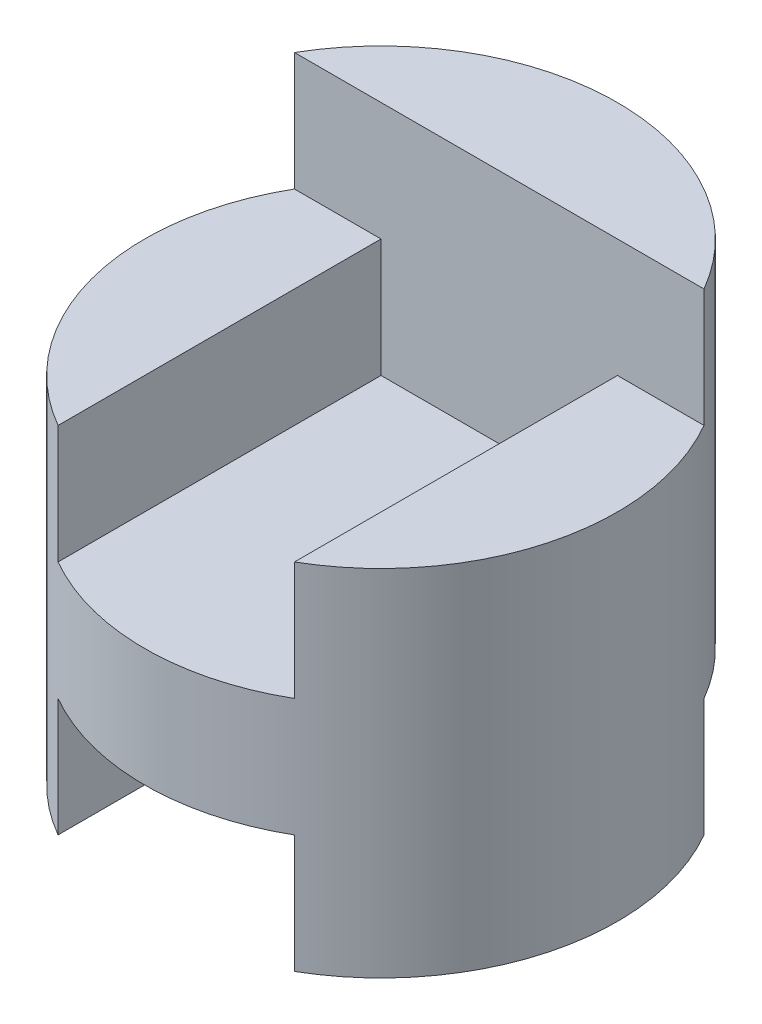
SolidWorks part; units mm, degrees
ref_plane "Front" through (0, 0, 0) normal (0, 0, 1) x (1, 0, 0)
ref_plane "Top" through (0, 0, 0) normal (0, 1, 0) x (1, 0, 0)
ref_plane "Right" through (0, 0, 0) normal (1, 0, 0) x (0, 0, -1)
sketch "Sketch1" plane through (0, 0, 0) normal (0, 1, 0) x (1, 0, 0)
  circle A0 centre (0, 0) radius 2
  dimension "D1" = 4
extrude "Boss-Extrude1" add sketch "Sketch1" along normal blind 4
sketch "Sketch2" plane through (0, 0, 0) normal (0, 0, 1) x (1, 0, 0)
  line L0 (-1, 1) -> (1, 1)
  line L4 (-1, 0) -> (-1, 1)
  line L16 (1, 0) -> (1, 1)
  line L17 (1, 0) -> (-1, 0)
  dimension "D4" = 1
extrude "Cut-Extrude1" cut sketch "Sketch2" against normal mid plane 4
sketch "Sketch3" plane through (0, 0, 0) normal (0, 0, 1) x (1, 0, 0)
  line L0 (-2, 4) -> (2, 4)
  line L1 (2, 4) -> (2, 3)
  line L2 (2, 0) -> (2, 4) construction
  line L7 (-1, 3) -> (-2, 3)
  line L8 (-2, 4) -> (-2, 0) construction
  line L9 (-2, 3) -> (-2, 4)
  line L17 (2, 3) -> (1, 3)
  line L18 (1, 3) -> (1, 2)
  line L19 (1, 2) -> (-1, 2)
  line L20 (-1, 2) -> (-1, 3)
  dimension "D1" = 1
  dimension "D2" = 1
  dimension "D3" = 2
  dimension "D4" = 1
  dimension "D5" = 1
extrude "Cut-Extrude2" cut sketch "Sketch3" against normal blind 1 and the other way blind 4
sketch "Sketch4" plane through (0, 0, 0) normal (1, 0, 0) x (0, 0, -1)
  line L0 (2, 1) -> (2, 4) construction
  line L1 (1.7321, 0) -> (1, 0)
  line L2 (1.7321, 0) -> (1.7321, 1)
  line L3 (1.7321, 1) -> (1, 1)
  line L4 (1, 0) -> (1, 1)
  point P7 (0, 0)
  dimension "D1" = 1
  dimension "D2" = 1
extrude "Cut-Extrude3" cut sketch "Sketch4" against normal mid plane 10
